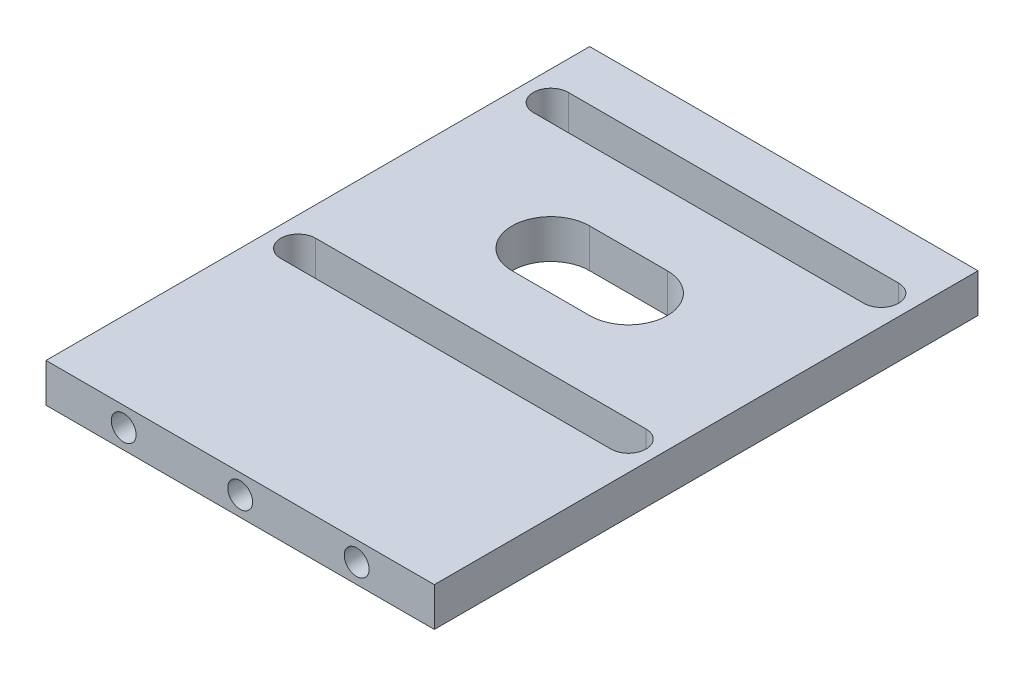
SolidWorks part; units mm, degrees
ref_plane "Front Plane" through (0, 0, 0) normal (0, 0, 1) x (1, 0, 0)
ref_plane "Top Plane" through (0, 0, 0) normal (0, 1, 0) x (1, 0, 0)
ref_plane "Right Plane" through (0, 0, 0) normal (1, 0, 0) x (0, 0, -1)
sketch "Sketch1" plane through (0, 0, 0) normal (0, 1, 0) x (1, 0, 0)
  line L0 (20.4249, 38.2744) -> (20.4249, -31.7256)
  line L1 (-29.5751, 38.2744) -> (20.4249, 38.2744)
  line L2 (-29.5751, 38.2744) -> (-29.5751, -31.7256)
  line L3 (-29.5751, -31.7256) -> (20.4249, -31.7256)
  line L5 (-25.8385, 29.5379) -> (16.6884, 29.5379) construction
  line L6 (-25.8385, 31.7879) -> (16.6884, 31.7879)
  line L7 (-25.8385, 27.2879) -> (16.6884, 27.2879)
  line L8 (-20.5751, 34.2744) -> (21.4249, 34.2744) construction
  line L9 (-20.5751, 34.2744) -> (-20.5751, -7.7256) construction
  line L10 (-20.5751, -7.7256) -> (21.4249, -7.7256) construction
  line L11 (21.4249, 34.2744) -> (21.4249, -7.7256) construction
  line L12 (-20.5751, 34.2744) -> (21.4249, -7.7256) construction
  line L13 (-20.5751, -7.7256) -> (21.4249, 34.2744) construction
  line L14 (-9.5751, 13.2744) -> (0.4249, 13.2744) construction
  line L15 (-9.5751, 13.2744) -> (0.4249, 13.2744) construction
  line L16 (-9.5751, 18.2744) -> (0.4249, 18.2744)
  line L17 (-9.5751, 8.2744) -> (0.4249, 8.2744)
  line L18 (-25.8385, -2.9891) -> (16.6884, -2.9891) construction
  line L19 (-25.8385, -5.2391) -> (16.6884, -5.2391)
  line L20 (-25.8385, -0.7391) -> (16.6884, -0.7391)
  circle A0 centre (0.4249, 13.2744) radius 23 construction
  circle A1 centre (-15.8385, 29.5379) radius 2.25 construction
  arc A2 (-25.8385, 31.7879) -> (-25.8385, 27.2879) centre (-25.8385, 29.5379) ccw
  arc A3 (16.6884, 27.2879) -> (16.6884, 31.7879) centre (16.6884, 29.5379) ccw
  circle A4 centre (0.4249, 13.2744) radius 4 construction
  arc A5 (-9.5751, 18.2744) -> (-9.5751, 8.2744) centre (-9.5751, 13.2744) ccw
  arc A6 (0.4249, 8.2744) -> (0.4249, 18.2744) centre (0.4249, 13.2744) ccw
  arc A7 (-25.8385, -5.2391) -> (-25.8385, -0.7391) centre (-25.8385, -2.9891) cw
  arc A8 (16.6884, -0.7391) -> (16.6884, -5.2391) centre (16.6884, -2.9891) cw
  point P0 (0, 0)
  point P6 (18.9384, 29.5379)
  point P7 (20.4249, 25.5063)
  point P8 (0.4249, 13.2744)
  point P9 (0.4249, 13.2744)
  point P18 (16.6884, 29.5379)
  point P19 (-25.8385, 29.5379)
  point P22 (-4.5751, 29.5379)
  point P28 (-9.5751, 13.2744)
  point P30 (-4.5751, 13.2744)
  point P37 (-4.5751, -2.9891)
  point P42 (-28.0885, 29.5379)
  dimension "D6" = 10
  dimension "D7" = 2.25
  dimension "D8" = 10
  dimension "D9" = 5
  dimension "D10" = 46
  dimension "D1" = 70
  dimension "D2" = 25
  dimension "D3" = 30
  dimension "D4" = 42
  dimension "D5" = 42
  dimension "D12" = 20
extrude "Boss-Extrude1" add sketch "Sketch1" along normal blind 5
sketch "Sketch2" plane through (0, 0, 31.7256) normal (0, 0, 1) x (1, 0, 0)
  line L0 (-29.5751, 2.5) -> (20.4249, 2.5) construction
  line L1 (-29.5751, 5) -> (-29.5751, 0) construction
  line L2 (20.4249, 5) -> (20.4249, 0) construction
  line L3 (-4.5751, 5) -> (-4.5751, 0) construction
  line L4 (-29.5751, 5) -> (20.4249, 5) construction
  line L5 (-29.5751, 0) -> (20.4249, 0) construction
  circle A0 centre (-4.5751, 2.5) radius 1.6
  circle A1 centre (-19.5751, 2.5) radius 1.6
  circle A2 centre (10.4249, 2.5) radius 1.6
  point P14 (-19.5751, 2.5)
  dimension "D1" = 10
extrude "Cut-Extrude1" cut sketch "Sketch2" against normal blind 10
